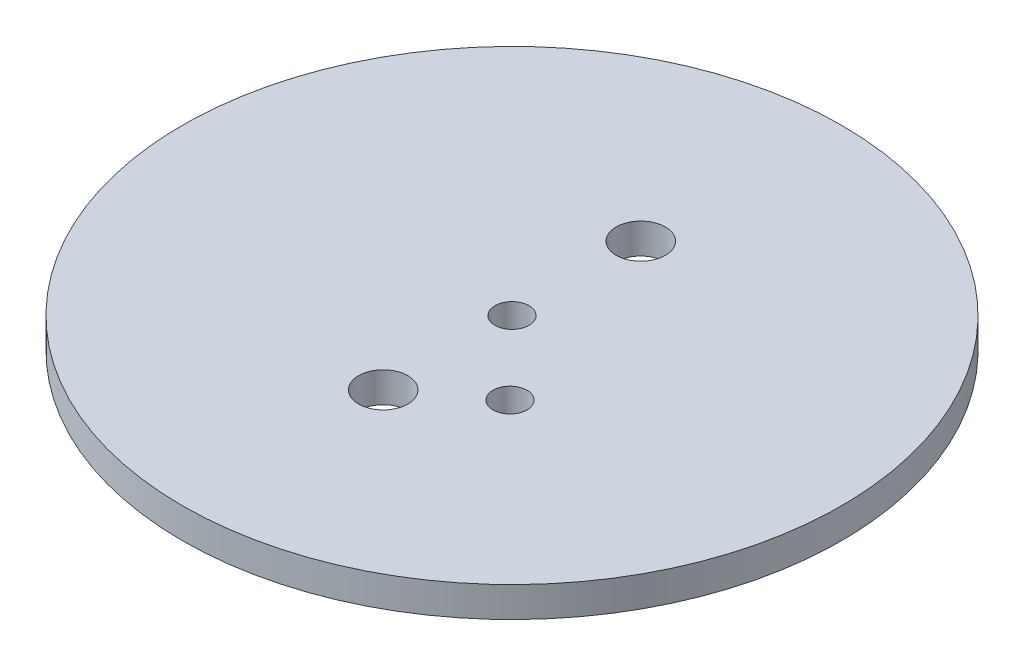
SolidWorks part; units mm, degrees
material "Chrome Stainless Steel"
ref_plane "Front Plane" through (0, 0, 0) normal (0, 0, 1) x (1, 0, 0)
ref_plane "Top Plane" through (0, 0, 0) normal (0, 1, 0) x (1, 0, 0)
ref_plane "Right Plane" through (0, 0, 0) normal (1, 0, 0) x (0, 0, -1)
sketch "Sketch1" plane through (0, 0, 0) normal (0, 1, 0) x (1, 0, 0)
  circle A0 centre (0, 0) radius 69.0563
  dimension "D1" = 138.1125
extrude "Boss-Extrude1" add sketch "Sketch1" along normal blind 6.35
hole_wizard "1/4 Clearance Hole1" positions "Sketch2" profile "Sketch3" hole size "1/4" standard "ANSI Inch" end condition through all
sketch "Sketch2" plane through (0, 6.35, 0) normal (0, 1, 0) x (1, 0, 0)
  point P0 (0, 0)
sketch "Sketch3" plane through (0, 6.35, 0) normal (1, 0, 0) x (0, 0, 1)
  line L0 (0, 0) -> (0, 6.35)
  line L1 (0, 6.35) -> (3.5712, 6.35)
  line L2 (3.5712, 6.35) -> (3.5712, 0)
  line L5 (3.5712, 0) -> (0, 0)
  line L11 (0, -6.35) -> (0, 107.95) construction
  dimension "Thru Hole Dia." = 7.1425
  dimension "Thru Hole Depth" = 6.35
hole_wizard "3/8 Clearance Hole1" positions "Sketch4" profile "Sketch5" hole size "3/8" standard "ANSI Inch" end condition through all
sketch "Sketch4" plane through (0, 6.35, 0) normal (0, 1, 0) x (1, 0, 0)
  line L0 (0, 26.9875) -> (0, -26.9875) construction
  point P0 (0, 26.9875)
  point P2 (0, -26.9875)
  point P9 (0, 0)
  dimension "D1" = 53.975
sketch "Sketch5" plane through (0, 6.35, -26.9875) normal (1, 0, 0) x (0, 0, 1)
  line L0 (0, 0) -> (0, 6.35)
  line L1 (0, 6.35) -> (5.1587, 6.35)
  line L2 (5.1587, 6.35) -> (5.1587, 0)
  line L5 (5.1587, 0) -> (0, 0)
  line L11 (0, -6.35) -> (0, 107.95) construction
  dimension "Thru Hole Dia." = 10.3175
  dimension "Thru Hole Depth" = 6.35
sketch "Sketch6" plane through (0, 6.35, 0) normal (0, 1, 0) x (1, 0, 0)
  circle A0 centre (15.1384, -15.5575) radius 3.5712
  circle A1 centre (0, -26.9875) radius 5.1587 construction
  dimension "D1" = 7.1425
  dimension "D2" = 15.1384
  dimension "D3" = 11.43
extrude "Cut-Extrude1" cut sketch "Sketch6" against normal up to surface (6.35 mm away) up to face at (0, 0, -21.8288)
